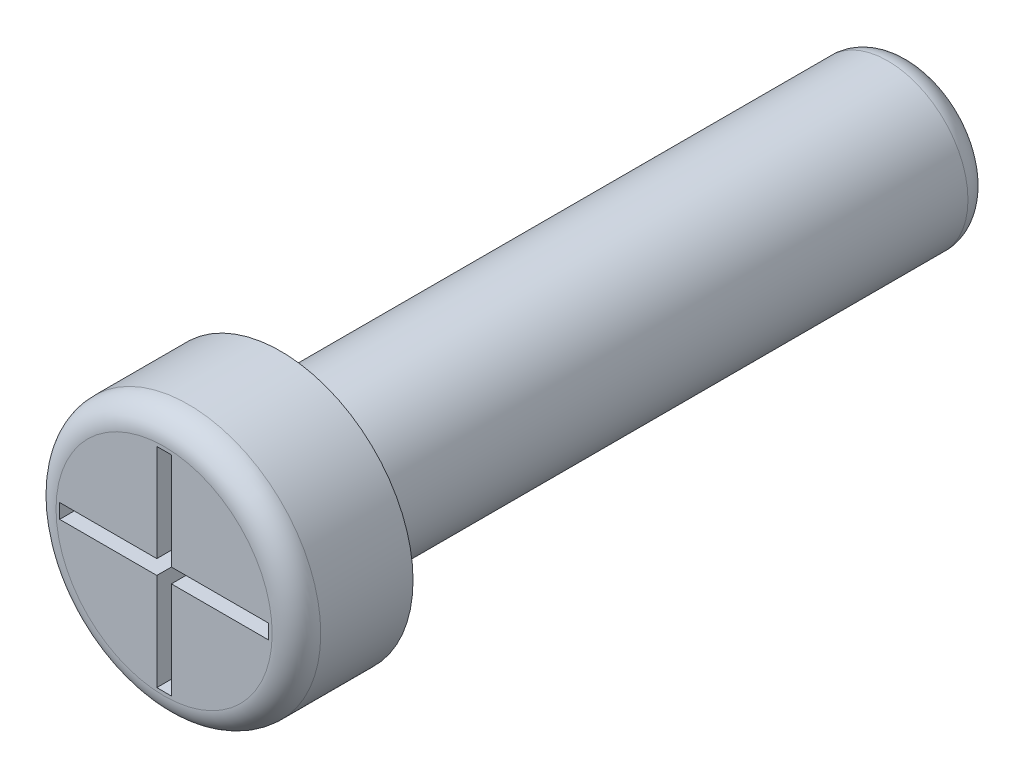
SolidWorks part; units mm, degrees
ref_plane "Přední rovina" through (0, 0, 0) normal (0, 0, 1) x (1, 0, 0)
ref_plane "Horní rovina" through (0, 0, 0) normal (0, 1, 0) x (1, 0, 0)
ref_plane "Pravá rovina" through (0, 0, 0) normal (1, 0, 0) x (0, 0, -1)
sketch "Skica1" plane through (0, 0, 0) normal (0, 0, 1) x (1, 0, 0)
  circle A0 centre (0, 0) radius 2.725
  dimension "D1" = 5.45
extrude "Přidat vysunutím1" add sketch "Skica1" along normal blind 2.4
sketch "Skica2" plane through (0, 0, 0) normal (0, 0, -1) x (-1, 0, 0)
  circle A0 centre (0, 0) radius 1.65
  dimension "D1" = 3.3
extrude "Přidat vysunutím3" add sketch "Skica2" along normal blind 13
sketch "Skica4" plane through (0, 0, 2.4) normal (0, 0, 1) x (1, 0, 0)
  line L0 (0, 0) -> (-0.15, 0) construction
  line L1 (-0.15, 0) -> (-0.15, 0.15) construction
  line L2 (-0.15, 0.15) -> (-0.15, 2.15)
  line L3 (-0.15, 2.15) -> (0.15, 2.15)
  line L4 (0.15, 2.15) -> (0.15, 0.15)
  line L5 (0.15, 0.15) -> (2.15, 0.15)
  line L6 (2.15, 0.15) -> (2.15, -0.15)
  line L7 (2.15, -0.15) -> (0.15, -0.15)
  line L8 (0.15, -0.15) -> (0.15, -2.15)
  line L9 (0.15, -2.15) -> (-0.15, -2.15)
  line L10 (-0.15, -2.15) -> (-0.15, -0.15)
  line L11 (-0.15, -0.15) -> (-2.15, -0.15)
  line L12 (-2.15, -0.15) -> (-2.15, 0.15)
  line L13 (-2.15, 0.15) -> (-0.15, 0.15)
  dimension "D1" = 0.15
  dimension "D2" = 0.15
  dimension "D3" = 2
  dimension "D4" = 2
  dimension "D5" = 2
  dimension "D6" = 2
  dimension "D7" = 0.3
  dimension "D8" = 2
  dimension "D9" = 2
  dimension "D10" = 0.3
  dimension "D11" = 0.3
extrude "Odebrat vysunutím1" cut sketch "Skica4" against normal blind 1
fillet "Zaoblit1" radius 0.5 2 edges at (2.725, 0, 2.4) (-1.65, 0, -13)
